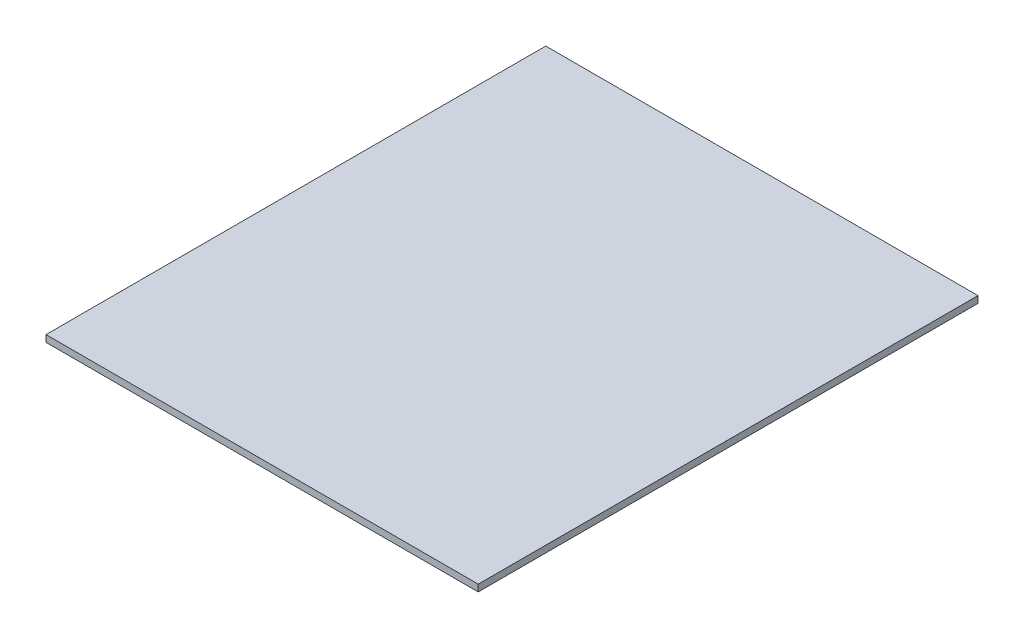
SolidWorks part; units mm, degrees
ref_plane "Front Plane" through (0, 0, 0) normal (0, 0, 1) x (1, 0, 0)
ref_plane "Top Plane" through (0, 0, 0) normal (0, 1, 0) x (1, 0, 0)
ref_plane "Right Plane" through (0, 0, 0) normal (1, 0, 0) x (0, 0, -1)
ref_plane "Plane1" through (441.9431, 255.6117, -503.9944) normal (1, 0, 0) x (0, 0, -1)
sketch3d "3DSketch1"
  line L2 (441.9431, 263.6117, 236.0056) -> (-198.0569, 263.6117, 236.0056)
  line L3 (441.9431, 263.6117, 236.0056) -> (441.9431, 263.6117, -503.9944)
  line L4 (441.9431, 263.6117, -503.9944) -> (-198.0569, 263.6117, -503.9944)
  line L5 (-198.0569, 263.6117, 236.0056) -> (-198.0569, 263.6117, -503.9944)
  line L6 (441.9431, 263.6117, 236.0056) -> (-198.0569, 263.6117, -503.9944) construction
  line L7 (441.9431, 263.6117, -503.9944) -> (-198.0569, 263.6117, 236.0056) construction
  point P0 (121.9431, 263.6117, -133.9944)
extrude "Boss-Extrude1" add sketch "3DSketch1" along a picked direction on the side of the normal blind 10
